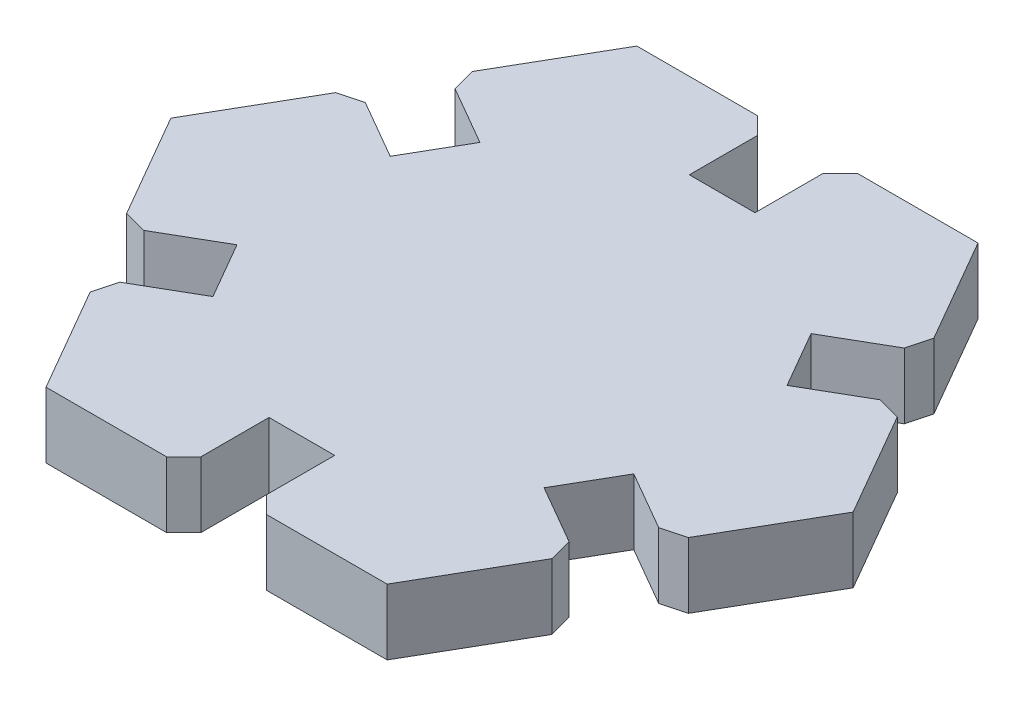
SolidWorks part; units mm, degrees
ref_plane "Front" through (0, 0, 0) normal (0, 0, 1) x (1, 0, 0)
ref_plane "Top" through (0, 0, 0) normal (0, 1, 0) x (1, 0, 0)
ref_plane "Right" through (0, 0, 0) normal (1, 0, 0) x (0, 0, -1)
sketch "Sketch1" plane through (0, 0, 0) normal (0, 1, 0) x (1, 0, 0)
  line L0 (0, 0) -> (20, 0) construction
  line L1 (20, 0) -> (10, 17.3205) construction
  line L2 (10, 17.3205) -> (-10, 17.3205) construction
  line L3 (-10, 17.3205) -> (-20, 0) construction
  line L4 (-20, 0) -> (-10, -17.3205) construction
  line L5 (-10, -17.3205) -> (10, -17.3205) construction
  line L6 (10, -17.3205) -> (20, 0) construction
  line L7 (0, 0) -> (15, 8.6603) construction
  line L8 (20, 0) -> (15.9625, 6.9932)
  line L9 (14.0375, 10.3274) -> (9.7074, 7.8274)
  line L10 (15.9625, 6.9932) -> (11.6324, 4.4932)
  line L11 (9.7074, 7.8274) -> (11.6324, 4.4932)
  line L12 (10, 17.3205) -> (14.0375, 10.3274)
  line L13 (10, -17.3205) -> (14.0375, -10.3274)
  line L14 (14.0375, -10.3274) -> (9.7074, -7.8274)
  line L15 (11.6324, -4.4932) -> (9.7074, -7.8274)
  line L16 (15.9625, -6.9932) -> (11.6324, -4.4932)
  line L17 (15.9625, -6.9932) -> (20, 0)
  line L18 (-10, -17.3205) -> (-1.925, -17.3205)
  line L19 (-1.925, -17.3205) -> (-1.925, -12.3205)
  line L20 (1.925, -12.3205) -> (-1.925, -12.3205)
  line L21 (1.925, -17.3205) -> (1.925, -12.3205)
  line L22 (1.925, -17.3205) -> (10, -17.3205)
  line L23 (-20, 0) -> (-15.9625, -6.9932)
  line L24 (-15.9625, -6.9932) -> (-11.6324, -4.4932)
  line L25 (-9.7074, -7.8274) -> (-11.6324, -4.4932)
  line L26 (-14.0375, -10.3274) -> (-9.7074, -7.8274)
  line L27 (-14.0375, -10.3274) -> (-10, -17.3205)
  line L28 (-10, 17.3205) -> (-14.0375, 10.3274)
  line L29 (-14.0375, 10.3274) -> (-9.7074, 7.8274)
  line L30 (-11.6324, 4.4932) -> (-9.7074, 7.8274)
  line L31 (-15.9625, 6.9932) -> (-11.6324, 4.4932)
  line L32 (-15.9625, 6.9932) -> (-20, 0)
  line L33 (10, 17.3205) -> (1.925, 17.3205)
  line L40 (1.925, 17.3205) -> (1.925, 12.3205)
  line L41 (-1.925, 12.3205) -> (1.925, 12.3205)
  line L42 (-1.925, 17.3205) -> (-1.925, 12.3205)
  line L43 (-1.925, 17.3205) -> (-10, 17.3205)
  circle A0 centre (0, 0) radius 17.3205 construction
  point P63 (0, 0)
  dimension "D1" = 3.85
  dimension "D2" = 5
  dimension "D3" = 20
  dimension "D5" = 240
  dimension "D6" = 240
  dimension "D7" = 240
  dimension "D8" = 240
  dimension "D9" = 240
  dimension "D10" = 240
  dimension "D11" = 34.641
  dimension "D4" = 6
extrude "Boss-Extrude1" add sketch "Sketch1" along normal blind 3.85 contours L15 L14 L13 L22 L21 L20 L19 L18 L27 L26 L25 L24 L23 L32 L31 L30 L29 L28 L43 L42 L41 L40 L33 L12 L9 L11 L10 L8 L17 L16
sketch "Sketch3" plane through (0, 0, 0) normal (0, 0, 1) x (1, 0, 0)
  line L0 (0, 0) -> (0, 54.119) construction
chamfer "Chamfer1" distance 1 angle 45 12 edges at (14.0375, 1.925, 10.3274) (15.9625, 1.925, 6.9932) (1.925, 1.925, 17.3205) (-1.925, 1.925, 17.3205) (-14.0375, 1.925, 10.3274) (-15.9625, 1.925, 6.9932) (-14.0375, 1.925, -10.3274) (-15.9625, 1.925, -6.9932) (15.9625, 1.925, -6.9932) (14.0375, 1.925, -10.3274) (1.925, 1.925, -17.3205) (-1.925, 1.925, -17.3205)
equation "\"entrance\"=5"
equation "\"D2@Sketch1\"=\"entrance\""
equation "\"D1@Sketch1\" = \"thick\""
equation "\"D1@Boss-Extrude1\"= \"thick\""
equation "\"thick\"=3.85"
